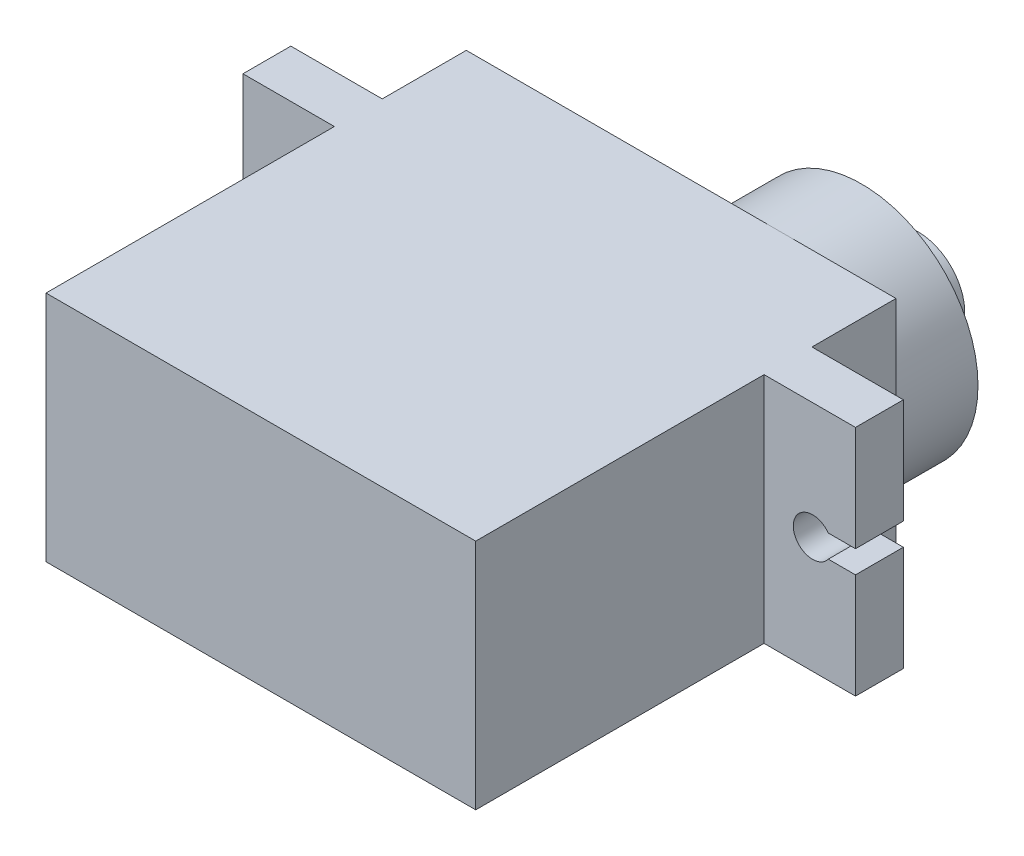
SolidWorks part; units mm, degrees
ref_plane "Front Plane" through (0, 0, 0) normal (0, 0, 1) x (1, 0, 0)
ref_plane "Top Plane" through (0, 0, 0) normal (0, 1, 0) x (1, 0, 0)
ref_plane "Right Plane" through (0, 0, 0) normal (1, 0, 0) x (0, 0, -1)
sketch "Sketch1" plane through (0, 0, 0) normal (0, 1, 0) x (1, 0, 0)
  line L1 (11.4, 11.15) -> (-11.4, 11.15)
  line L2 (11.4, 11.15) -> (11.4, -11.15)
  line L3 (11.4, -11.15) -> (-11.4, -11.15)
  line L4 (-11.4, 11.15) -> (-11.4, -11.15)
  line L5 (11.4, 11.15) -> (-11.4, -11.15) construction
  line L6 (11.4, -11.15) -> (-11.4, 11.15) construction
  point P0 (0, 0)
  dimension "D1" = 22.8
  dimension "D2" = 22.3
extrude "Boss-Extrude1" add sketch "Sketch1" along normal mid plane 12.35
sketch "Sketch2" plane through (11.4, 0, 0) normal (1, 0, 0) x (0, 0, -1)
  line L0 (-11.15, 6.175) -> (11.15, 6.175) construction
  line L1 (4.15, 6.175) -> (6.69, 6.175)
  line L2 (4.15, 6.175) -> (4.15, -6.175)
  line L3 (4.15, -6.175) -> (6.69, -6.175)
  line L4 (6.69, 6.175) -> (6.69, -6.175)
  line L5 (-11.15, -6.175) -> (11.15, -6.175) construction
  line L6 (11.15, 6.175) -> (11.15, -6.175) construction
  dimension "D1" = 7
  dimension "D2" = 2.54
extrude "Boss-Extrude2" add sketch "Sketch2" along normal blind 4.85
mirror "Mirror1" about plane through (0, 0, 0) normal (1, 0, 0) of "Boss-Extrude2"
sketch "Sketch3" plane through (0, 0, -6.69) normal (0, 0, -1) x (-1, 0, 0)
  line L0 (-13.975, 0) -> (13.975, 0) construction
  line L1 (-14.806, 0.6) -> (-16.25, 0.6)
  line L2 (-16.25, -6.175) -> (-16.25, 6.175) construction
  line L3 (-16.25, 0.6) -> (-16.25, -0.6)
  line L4 (-16.25, -0.6) -> (-14.806, -0.6)
  line L5 (14.806, 0.6) -> (16.25, 0.6)
  line L6 (16.25, -6.175) -> (16.25, 6.175) construction
  line L7 (16.25, 0.6) -> (16.25, -0.6)
  line L8 (16.25, -0.6) -> (14.806, -0.6)
  arc A0 (-14.806, -0.6) -> (-14.806, 0.6) centre (-13.975, 0) ccw
  arc A1 (14.806, 0.6) -> (14.806, -0.6) centre (13.975, 0) ccw
  point P4 (0, 0)
  point P6 (-12.95, 0)
  point P7 (12.95, 0)
  dimension "D1" = 2.05
  dimension "D2" = 25.9
  dimension "D3" = 1.2
extrude "Cut-Extrude1" cut sketch "Sketch3" against normal through all
sketch "Sketch4" plane through (0, 0, -11.15) normal (0, 0, -1) x (-1, 0, 0)
  line L0 (-11.4, -6.175) -> (-11.4, 6.175) construction
  line L1 (-11.4, 6.175) -> (11.4, 6.175) construction
  circle A0 centre (-5.225, 0) radius 6.175
extrude "Boss-Extrude3" add sketch "Sketch4" along normal blind 4.35
sketch "Sketch5" plane through (0, 0, -15.5) normal (0, 0, -1) x (-1, 0, 0)
  circle A0 centre (-5.225, 0) radius 2.475
  dimension "D1" = 4.95
extrude "Boss-Extrude4" add sketch "Sketch5" along normal blind 3
sketch "Sketch6" plane through (0, 0, -18.5) normal (0, 0, -1) x (-1, 0, 0)
  circle A0 centre (-5.225, 0) radius 0.9
  dimension "D1" = 1.8
extrude "Cut-Extrude2" cut sketch "Sketch6" against normal blind 2
